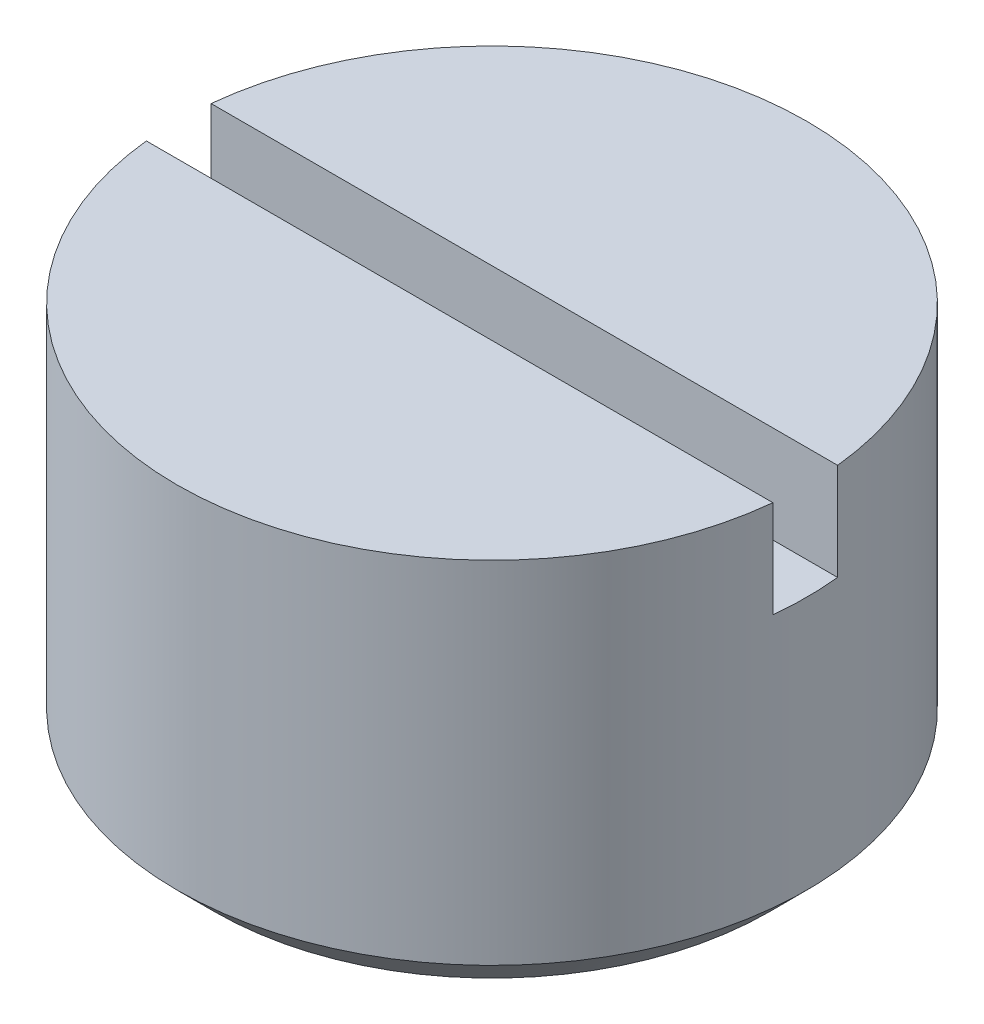
SolidWorks part; units mm, degrees
ref_plane "Front Plane" through (0, 0, 0) normal (0, 0, 1) x (1, 0, 0)
ref_plane "Top Plane" through (0, 0, 0) normal (0, 1, 0) x (1, 0, 0)
ref_plane "Right Plane" through (0, 0, 0) normal (1, 0, 0) x (0, 0, -1)
ref_plane "Plane1" through (0, 0, 0) normal (0, 0, 1) x (1, 0, 0)
sketch "Sketch1" plane through (0, 0, 0) normal (0, 0, 1) x (1, 0, 0)
  line L0 (0, 0) -> (4.864, 0)
  line L1 (4.864, 0) -> (4.864, -5.419)
  line L2 (4.864, -5.419) -> (4.283, -6)
  line L3 (4.283, -6) -> (0, -6)
  line L4 (0, -6) -> (0, 0)
  line L5 (0, -6) -> (0, 0) construction
revolve "Revolve1" add sketch "Sketch1" angle 360 about L5
cosmetic thread "Cosmetic Thread1" parameters "D1"=6, "D2"=8.566
ref_plane "Plane2" through (0, 0, 0) normal (0, 1, 0) x (1, 0, 0)
sketch "Sketch2" plane through (0, 0, 0) normal (0, 1, 0) x (1, 0, 0)
  line L0 (-4.864, 0.5) -> (-4.864, -0.5)
  line L1 (-4.864, -0.5) -> (4.864, -0.5)
  line L2 (4.864, -0.5) -> (4.864, 0.5)
  line L3 (4.864, 0.5) -> (-4.864, 0.5)
extrude "Cut-Extrude1" cut sketch "Sketch2" against normal blind 1.5
